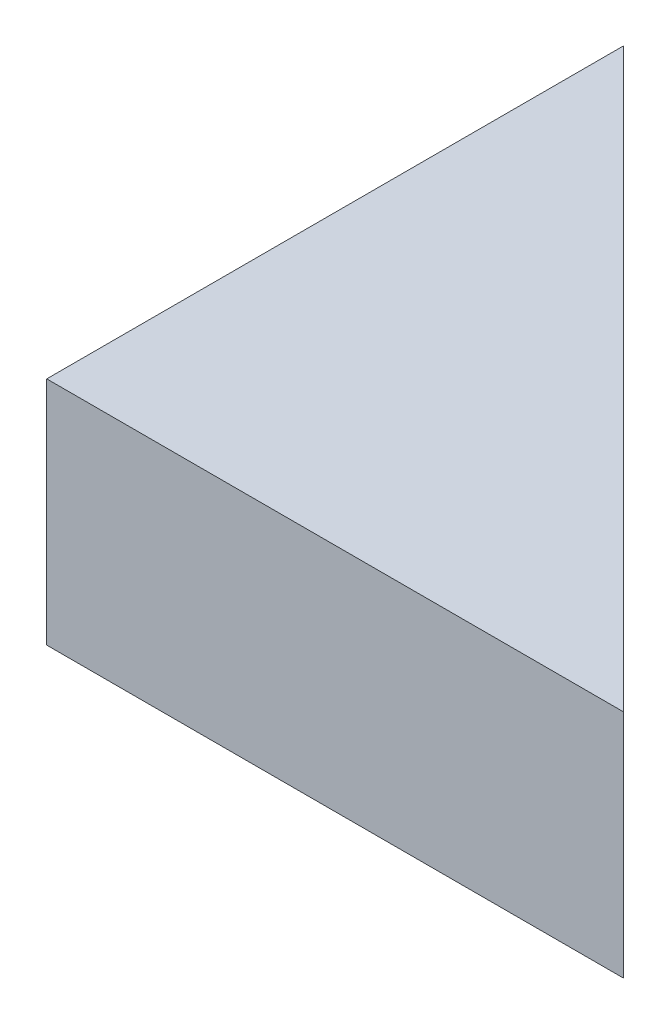
SolidWorks part; units mm, degrees
ref_plane "Alzado" through (0, 0, 0) normal (0, 0, 1) x (1, 0, 0)
ref_plane "Planta" through (0, 0, 0) normal (0, 1, 0) x (1, 0, 0)
ref_plane "Vista lateral" through (0, 0, 0) normal (1, 0, 0) x (0, 0, -1)
sketch "Croquis1" plane through (0, 0, 0) normal (0, 1, 0) x (1, 0, 0)
  line L0 (0, 0) -> (0, 500)
  line L1 (0, 500) -> (500, 0)
  line L2 (500, 0) -> (0, 0)
  dimension "D1" = 500
  dimension "D2" = 500
extrude "Saliente-Extruir1" add sketch "Croquis1" along normal blind 200
